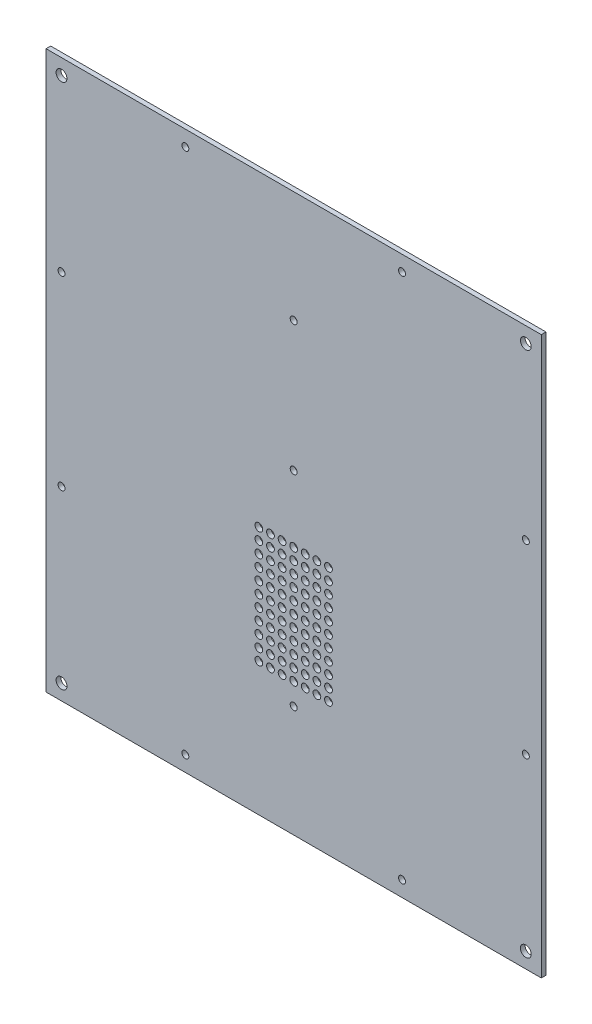
SolidWorks part; units mm, degrees
ref_plane "Спереди" through (0, 0, 0) normal (0, 0, 1) x (1, 0, 0)
ref_plane "Сверху" through (0, 0, 0) normal (0, 1, 0) x (1, 0, 0)
ref_plane "Справа" through (0, 0, 0) normal (1, 0, 0) x (0, 0, -1)
sketch "Эскиз1" plane through (0, 0, 0) normal (0, 0, 1) x (1, 0, 0)
  line L0 (0, 0) -> (320, 0)
  line L1 (0, 0) -> (0, 360)
  line L2 (320, 0) -> (320, 360)
  line L3 (0, 360) -> (320, 360)
  line L4 (10, 350) -> (310, 350) construction
  line L5 (10, 350) -> (10, 10) construction
  line L6 (310, 350) -> (310, 10) construction
  line L7 (10, 10) -> (310, 10) construction
  line L8 (0, 360) -> (20, 360) construction
  line L9 (0, 360) -> (0, 340) construction
  line L10 (20, 360) -> (20, 340) construction
  line L11 (0, 340) -> (20, 340) construction
  line L12 (160, 350) -> (160, 10) construction
  line L17 (320, 360) -> (300, 360) construction
  line L18 (320, 360) -> (320, 340) construction
  line L19 (300, 360) -> (300, 340) construction
  line L20 (320, 340) -> (300, 340) construction
  circle A0 centre (90, 10) radius 2.25
  circle A1 centre (90, 350) radius 2.25
  circle A2 centre (230, 350) radius 2.25
  circle A3 centre (230, 10) radius 2.25
  circle A4 centre (10, 240) radius 2.25
  circle A5 centre (10, 120) radius 2.25
  circle A6 centre (310, 240) radius 2.25
  circle A7 centre (310, 120) radius 2.25
  dimension "D9" = 90
  dimension "D10" = 90
  dimension "D11" = 4.5
  dimension "D12" = 140
  dimension "D13" = 4.5
  dimension "D14" = 70
  dimension "D15" = 4.5
  dimension "D16" = 4.5
  dimension "D20" = 4.5
  dimension "D21" = 120
  dimension "D22" = 120
  dimension "D23" = 120
  dimension "D24" = 4.5
  dimension "D25" = 4.5
  dimension "D26" = 120
  dimension "D27" = 120
  dimension "D19" = 4.5
  dimension "D1" = 360
  dimension "D2" = 320
  dimension "D3" = 10
  dimension "D4" = 10
  dimension "D5" = 10
  dimension "D6" = 10
  dimension "D7" = 20
  dimension "D8" = 20
  dimension "D18" = 90
  dimension "D28" = 20
  dimension "D29" = 20
  dimension "D17" = 90
extrude "Бобышка-Вытянуть1" add sketch "Эскиз1" along normal blind 3
sketch "Эскиз2" plane through (0, 0, 3) normal (0, 0, 1) x (1, 0, 0)
  line L0 (320, 360) -> (0, 360) construction
  line L1 (0, 360) -> (0, 0) construction
  line L2 (10, 350) -> (310, 350) construction
  line L3 (10, 350) -> (10, 10) construction
  line L4 (310, 350) -> (310, 10) construction
  line L5 (10, 10) -> (310, 10) construction
  line L6 (320, 0) -> (320, 360) construction
  line L7 (0, 0) -> (320, 0) construction
  circle A0 centre (10, 350) radius 3.5
  circle A1 centre (310, 350) radius 3.5
  circle A2 centre (310, 10) radius 3.5
  circle A3 centre (10, 10) radius 3.5
  dimension "D1" = 10
  dimension "D2" = 10
  dimension "D3" = 7
  dimension "D4" = 10
  dimension "D6" = 7
  dimension "D7" = 7
  dimension "D8" = 7
  dimension "D5" = 10
extrude "Вырез-Вытянуть1" cut sketch "Эскиз2" against normal through all
sketch "Эскиз3" plane through (0, 0, 3) normal (0, 0, 1) x (1, 0, 0)
  line L4 (0, 360) -> (0, 0)
  line L5 (0, 0) -> (320, 0)
  line L6 (320, 0) -> (320, 360)
  line L7 (320, 360) -> (0, 360)
  line L8 (0, 360) -> (0, 0)
  line L9 (0, 0) -> (320, 0)
  line L10 (320, 0) -> (320, 360)
  line L11 (320, 360) -> (0, 360)
  dimension "D1" = 0
sketch "Эскиз4" plane through (0, 0, 3) normal (0, 0, 1) x (1, 0, 0)
  line L0 (300, 72) -> (20, 72) construction
  line L1 (300, 72) -> (20, 72) construction
  line L2 (300, 204) -> (20, 204) construction
  line L3 (300, 204) -> (20, 204) construction
  line L4 (300, 288) -> (20, 288) construction
  line L5 (300, 288) -> (20, 288) construction
  line L6 (185, 83.5) -> (135, 83.5) construction
  line L7 (185, 83.5) -> (185, 164) construction
  line L8 (135, 83.5) -> (135, 164) construction
  line L9 (185, 164) -> (135, 164) construction
  line L10 (160, 83.5) -> (160, 164) construction
  line L11 (160, 83.5) -> (160, 72) construction
  line L12 (135, 86) -> (185, 86) construction
  line L13 (137.5, 86) -> (137.5, 164) construction
  circle A0 centre (160, 288) radius 2.25
  circle A1 centre (160, 204) radius 2.25
  circle A2 centre (160, 72) radius 2.25
  circle A3 centre (137.5, 86) radius 2.5
  circle A4 centre (145, 86) radius 2.5
  circle A5 centre (152.5, 86) radius 2.5
  circle A6 centre (160, 86) radius 2.5
  circle A7 centre (167.5, 86) radius 2.5
  circle A8 centre (175, 86) radius 2.5
  circle A9 centre (182.5, 86) radius 2.5
  circle A10 centre (137.5, 93.5) radius 2.5
  circle A11 centre (145, 93.5) radius 2.5
  circle A12 centre (152.5, 93.5) radius 2.5
  circle A13 centre (160, 93.5) radius 2.5
  circle A14 centre (167.5, 93.5) radius 2.5
  circle A15 centre (175, 93.5) radius 2.5
  circle A16 centre (182.5, 93.5) radius 2.5
  circle A17 centre (137.5, 101) radius 2.5
  circle A18 centre (145, 101) radius 2.5
  circle A19 centre (152.5, 101) radius 2.5
  circle A20 centre (160, 101) radius 2.5
  circle A21 centre (167.5, 101) radius 2.5
  circle A22 centre (175, 101) radius 2.5
  circle A23 centre (182.5, 101) radius 2.5
  circle A24 centre (137.5, 108.5) radius 2.5
  circle A25 centre (145, 108.5) radius 2.5
  circle A26 centre (152.5, 108.5) radius 2.5
  circle A27 centre (160, 108.5) radius 2.5
  circle A28 centre (167.5, 108.5) radius 2.5
  circle A29 centre (175, 108.5) radius 2.5
  circle A30 centre (182.5, 108.5) radius 2.5
  circle A31 centre (137.5, 116) radius 2.5
  circle A32 centre (145, 116) radius 2.5
  circle A33 centre (152.5, 116) radius 2.5
  circle A34 centre (160, 116) radius 2.5
  circle A35 centre (167.5, 116) radius 2.5
  circle A36 centre (175, 116) radius 2.5
  circle A37 centre (182.5, 116) radius 2.5
  circle A38 centre (137.5, 123.5) radius 2.5
  circle A39 centre (145, 123.5) radius 2.5
  circle A40 centre (152.5, 123.5) radius 2.5
  circle A41 centre (160, 123.5) radius 2.5
  circle A42 centre (167.5, 123.5) radius 2.5
  circle A43 centre (175, 123.5) radius 2.5
  circle A44 centre (182.5, 123.5) radius 2.5
  circle A45 centre (137.5, 131) radius 2.5
  circle A46 centre (145, 131) radius 2.5
  circle A47 centre (152.5, 131) radius 2.5
  circle A48 centre (160, 131) radius 2.5
  circle A49 centre (167.5, 131) radius 2.5
  circle A50 centre (175, 131) radius 2.5
  circle A51 centre (182.5, 131) radius 2.5
  circle A52 centre (137.5, 138.5) radius 2.5
  circle A53 centre (145, 138.5) radius 2.5
  circle A54 centre (152.5, 138.5) radius 2.5
  circle A55 centre (160, 138.5) radius 2.5
  circle A56 centre (167.5, 138.5) radius 2.5
  circle A57 centre (175, 138.5) radius 2.5
  circle A58 centre (182.5, 138.5) radius 2.5
  circle A59 centre (137.5, 146) radius 2.5
  circle A60 centre (145, 146) radius 2.5
  circle A61 centre (152.5, 146) radius 2.5
  circle A62 centre (160, 146) radius 2.5
  circle A63 centre (167.5, 146) radius 2.5
  circle A64 centre (175, 146) radius 2.5
  circle A65 centre (182.5, 146) radius 2.5
  circle A66 centre (137.5, 153.5) radius 2.5
  circle A67 centre (145, 153.5) radius 2.5
  circle A68 centre (152.5, 153.5) radius 2.5
  circle A69 centre (160, 153.5) radius 2.5
  circle A70 centre (167.5, 153.5) radius 2.5
  circle A71 centre (175, 153.5) radius 2.5
  circle A72 centre (182.5, 153.5) radius 2.5
  circle A73 centre (137.5, 161) radius 2.5
  circle A74 centre (145, 161) radius 2.5
  circle A75 centre (152.5, 161) radius 2.5
  circle A76 centre (160, 161) radius 2.5
  circle A77 centre (167.5, 161) radius 2.5
  circle A78 centre (175, 161) radius 2.5
  circle A79 centre (182.5, 161) radius 2.5
  dimension "D1" = 4.5
  dimension "D5" = 5
  dimension "D7" = 7.5
  dimension "D9" = 7.5
  dimension "D2" = 50
  dimension "D3" = 11.5
  dimension "D4" = 40
  dimension "D6" = 7
  dimension "D8" = 11
extrude "Вырез-Вытянуть2" cut sketch "Эскиз4" against normal through all
